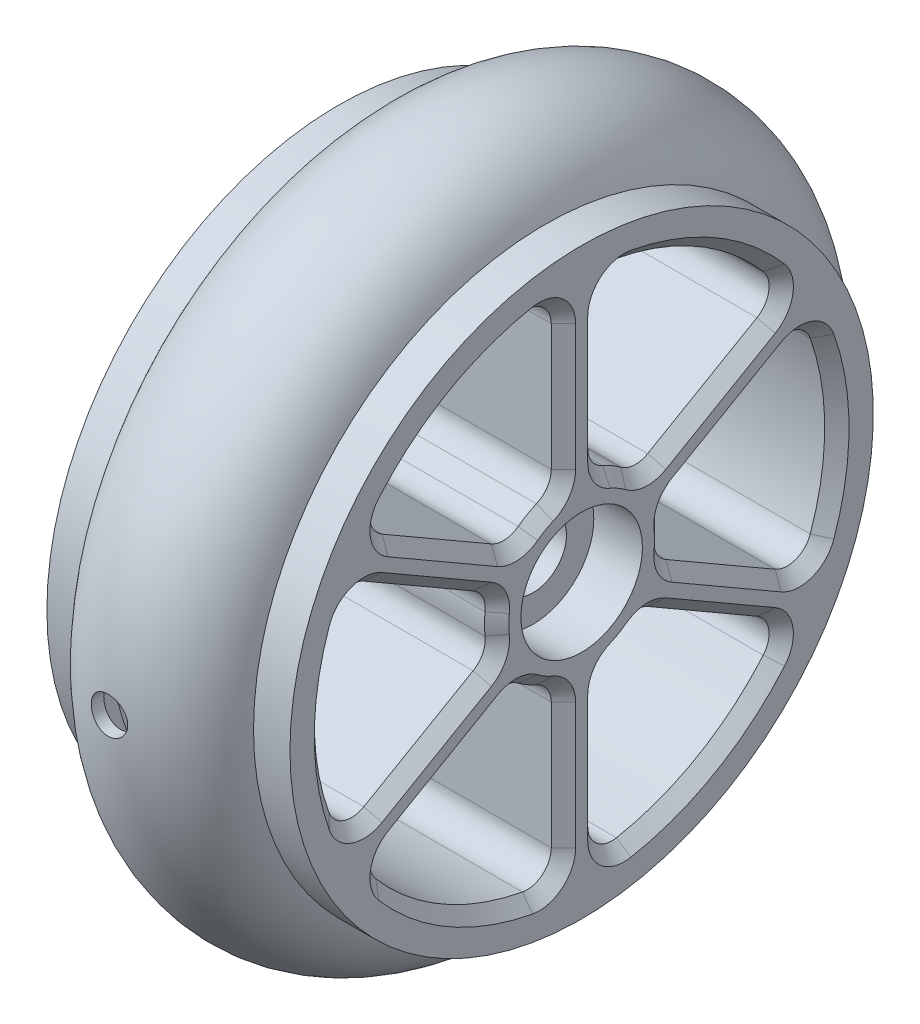
SolidWorks part; units mm, degrees
ref_plane "Front Plane" through (0, 0, 0) normal (0, 0, 1) x (1, 0, 0)
ref_plane "Top Plane" through (0, 0, 0) normal (0, 1, 0) x (1, 0, 0)
ref_plane "Right Plane" through (0, 0, 0) normal (1, 0, 0) x (0, 0, -1)
sketch "Sketch1" plane through (0, 0, 0) normal (0, 0, 1) x (1, 0, 0)
  line L14 (-10, 24) -> (-10, 0)
  line L15 (-10, 0) -> (10, 0)
  line L16 (-29.6857, 0) -> (25.2979, 0) construction
  line L17 (10, 0) -> (10, 24)
  line L18 (0, 29.9527) -> (0, -13.4426) construction
  line L19 (-10, 24) -> (-7, 24)
  line L20 (10, 24) -> (7, 24)
  arc A0 (7, 24) -> (-7, 24) centre (0, 21.6) ccw
  point P7 (0, 29)
  dimension "D2" = 14
  dimension "D1" = 20
  dimension "D3" = 48
  dimension "D4" = 58
revolve "Revolve1" add sketch "Sketch1" angle 360 about L16
sketch "Sketch2" plane through (10, 0, 0) normal (1, 0, 0) x (0, 0, -1)
  circle A0 centre (0, 0) radius 2.75
  dimension "D1" = 5.5
extrude "Cut-Extrude1" cut sketch "Sketch2" against normal up to next
sketch "Sketch3" plane through (-10, 0, 0) normal (-1, 0, 0) x (0, 0, 1)
  circle A0 centre (0, 0) radius 5
  dimension "D1" = 10
extrude "Cut-Extrude2" cut sketch "Sketch3" against normal blind 4
sketch "Sketch4" plane through (10, 0, 0) normal (1, 0, 0) x (0, 0, -1)
  circle A0 centre (0, 0) radius 5
  circle A1 centre (0, 0) radius 5 construction
extrude "Cut-Extrude3" cut sketch "Sketch4" against normal blind 4
sketch "Sketch5" plane through (10, 0, 0) normal (1, 0, 0) x (0, 0, -1)
  line L0 (-18.1865, 10.5) -> (18.1865, -10.5) construction
  line L1 (0, -21) -> (18.1865, -10.5)
  line L2 (18.1865, -10.5) -> (18.1865, 10.5)
  line L3 (18.1865, 10.5) -> (0, 21)
  line L4 (0, 21) -> (-18.1865, 10.5)
  line L5 (-18.1865, 10.5) -> (-18.1865, -10.5)
  line L6 (-18.1865, -10.5) -> (0, -21)
  line L7 (18.1865, 10.5) -> (-18.1865, -10.5) construction
  line L8 (0, 21) -> (0, -21) construction
  line L9 (-1.5, 21) -> (-1.5, -21)
  line L10 (17.4365, 11.799) -> (-18.9365, -9.201)
  line L11 (-18.9365, 9.201) -> (17.4365, -11.799)
  line L12 (1.5, 21) -> (1.5, -21)
  line L13 (18.9365, 9.201) -> (-17.4365, -11.799)
  line L14 (-17.4365, 11.799) -> (18.9365, -9.201)
  circle A0 centre (0, 0) radius 5 construction
  circle A1 centre (0, 0) radius 24 construction
  circle A3 centre (0, 0) radius 7
  circle A5 centre (0, 0) radius 21
  circle A6 centre (0, 0) radius 18.1865 construction
  dimension "D1" = 3
  dimension "D4" = 2
  dimension "D2" = 1.5
  dimension "D3" = 1.5
extrude "Cut-Extrude4" cut sketch "Sketch5" against normal up to next
fillet "Fillet2" radius 2 24 edges at (0, 11.7722, -17.3901) (0, -9.1741, 18.8901) (0, 4.7177, -5.1714) (0, -2.1197, 6.6714) (0, -6.8374, -1.5) (0, 6.8374, -1.5) (0, -20.9464, -1.5) (0, 20.9464, -1.5) (0, -20.9464, 1.5) (0, 20.9464, 1.5) (0, -9.1741, -18.8901) (0, 11.7722, 17.3901) (0, -2.1197, -6.6714) (0, 4.7177, 5.1714) (0, -6.8374, 1.5) (0, 6.8374, 1.5) (0, -11.7722, -17.3901) (0, 9.1741, 18.8901) (0, -4.7177, -5.1714) (0, 2.1197, 6.6714) (0, -4.7177, 5.1714) (0, 2.1197, -6.6714) (0, -11.7722, 17.3901) (0, 9.1741, -18.8901)
chamfer "Chamfer1" distance 1 angle 45 48 edges at (10, 6.0622, 3.5) (10, 7.186, 1.8333) (10, 5.1807, 5.3066) (10, 13.4832, 1.5) (10, 8.0406, 10.9268) (10, 20.2138, 2.2227) (10, 12.0318, 16.3943) (10, 18.1865, 10.5) (10, 0, 7) (10, 2.0053, 7.1399) (10, -2.0053, 7.1399) (10, 5.4426, 12.4268) (10, -5.4426, 12.4268) (10, 8.182, 18.617) (10, -8.182, 18.617) (10, 0, 21) (10, -6.0622, 3.5) (10, -5.1807, 5.3066) (10, -7.186, 1.8333) (10, -8.0406, 10.9268) (10, -13.4832, 1.5) (10, -12.0318, 16.3943) (10, -20.2138, 2.2227) (10, -18.1865, 10.5) (10, -6.0622, -3.5) (10, -7.186, -1.8333) (10, -5.1807, -5.3066) (10, -13.4832, -1.5) (10, -8.0406, -10.9268) (10, -20.2138, -2.2227) (10, -12.0318, -16.3943) (10, -18.1865, -10.5) (10, 0, -7) (10, -2.0053, -7.1399) (10, 2.0053, -7.1399) (10, -5.4426, -12.4268) (10, 5.4426, -12.4268) (10, -8.182, -18.617) (10, 8.182, -18.617) (10, 0, -21) (10, 6.0622, -3.5) (10, 5.1807, -5.3066) (10, 7.186, -1.8333) (10, 8.0406, -10.9268) (10, 13.4832, -1.5) (10, 12.0318, -16.3943) (10, 20.2138, -2.2227) (10, 18.1865, -10.5)
sketch "Sketch8" plane through (0, 0, 0) normal (0, 0, 1) x (1, 0, 0)
  line L0 (-7, 24) -> (-7, -24) construction
  line L1 (7, 24) -> (7, -24) construction
  line L2 (-7, 24) -> (-7, -24)
  line L3 (7, 24) -> (7, -24)
  line L4 (-6, 23.8271) -> (-6, -23.8271)
  line L5 (6, 23.8271) -> (6, -23.8271)
  line L6 (-6, 22.8271) -> (6, 22.8271)
  line L7 (-25.0311, 0) -> (27.3418, 0) construction
  arc A0 (7, 24) -> (-7, 24) centre (0, 21.6) ccw construction
  arc A1 (7, 24) -> (-7, 24) centre (0, 21.6) ccw
  arc A2 (-7, -24) -> (7, -24) centre (0, -21.6) ccw construction
  arc A3 (-7, -24) -> (7, -24) centre (0, -21.6) ccw
  arc A4 (6, 23.8271) -> (-6, 23.8271) centre (0, 21.6) ccw
  arc A5 (-6, -23.8271) -> (6, -23.8271) centre (0, -21.6) ccw
  dimension "D2" = 1
  dimension "D1" = 1
revolve "Cut-Revolve1" cut sketch "Sketch8" angle 360 about L7
ref_plane "Plane1" through (0, 0, 15) normal (0, 0, 1) x (1, 0, 0)
sketch "Sketch9" plane through (0, 0, 15) normal (0, 0, 1) x (1, 0, 0)
  circle A0 centre (0, 0) radius 1.5
  dimension "D1" = 3
extrude "Cut-Extrude6" cut sketch "Sketch9" along normal up to surface (13.8464 mm away)
mirror "Mirror1" about plane through (0, 0, 0) normal (0, 0, 1) of "Cut-Extrude6"
sketch "Sketch7" plane through (-6, 0, 0) normal (-1, 0, 0) x (0, 0, 1)
  circle A1 centre (0, 0) radius 5
  circle A2 centre (0, 0) radius 5
  dimension "D1" = 0
extrude "Cut-Extrude5" cut sketch "Sketch7" against normal blind 0.5
